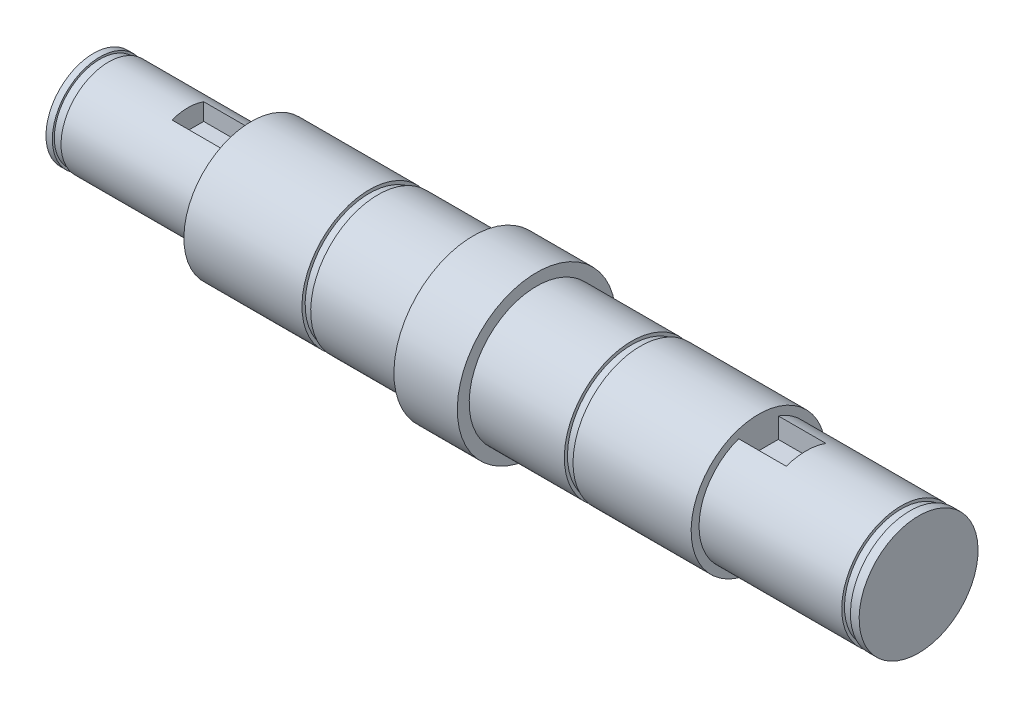
SolidWorks part; units mm, degrees
ref_plane "Front Plane" through (0, 0, 0) normal (0, 0, 1) x (1, 0, 0)
ref_plane "Top Plane" through (0, 0, 0) normal (0, 1, 0) x (1, 0, 0)
ref_plane "Right Plane" through (0, 0, 0) normal (1, 0, 0) x (0, 0, -1)
sketch "Sketch1" plane through (0, 0, 0) normal (0, 0, 1) x (1, 0, 0)
  line L0 (-52.05, 0) -> (52.05, 0)
  line L17 (-52.05, 0) -> (-52.05, 6)
  line L18 (-52.05, 6) -> (-51.25, 6)
  line L19 (-32.15, 6) -> (-32.15, 8.5)
  line L20 (-32.15, 8.5) -> (-17.25, 8.5)
  line L22 (-4.15, 8.5) -> (-4.15, 10)
  line L23 (-4.15, 10) -> (3.85, 10)
  line L24 (3.85, 10) -> (3.85, 8.5)
  line L25 (3.85, 8.5) -> (15.85, 8.5)
  line L26 (31.85, 8.5) -> (31.85, 7.5)
  line L27 (31.85, 7.5) -> (49.85, 7.5)
  line L28 (52.05, 7.5) -> (52.05, 0)
  line L29 (-50.15, 6) -> (-32.15, 6)
  line L31 (-51.25, 6) -> (-51.25, 5.75)
  line L32 (-51.25, 5.75) -> (-50.15, 5.75)
  line L33 (-50.15, 6) -> (-50.15, 5.75)
  line L34 (50.95, 7.5) -> (52.05, 7.5)
  line L36 (49.85, 7.5) -> (49.85, 7.15)
  line L37 (49.85, 7.15) -> (50.95, 7.15)
  line L38 (50.95, 7.5) -> (50.95, 7.15)
  line L39 (-16.15, 8.5) -> (-4.15, 8.5)
  line L41 (-17.25, 8.5) -> (-17.25, 8.1)
  line L42 (-17.25, 8.1) -> (-16.15, 8.1)
  line L43 (-16.15, 8.5) -> (-16.15, 8.1)
  line L44 (16.95, 8.5) -> (31.85, 8.5)
  line L46 (15.85, 8.5) -> (15.85, 8.1)
  line L47 (15.85, 8.1) -> (16.95, 8.1)
  line L48 (16.95, 8.5) -> (16.95, 8.1)
  point P4 (0, 0)
  dimension "D1" = 104.1
  dimension "D2" = 6
  dimension "D3" = 8.5
  dimension "D4" = 10
  dimension "D5" = 8.5
  dimension "D6" = 7.5
  dimension "D7" = 19.9
  dimension "D8" = 28
  dimension "D9" = 8
  dimension "D10" = 28
  dimension "D11" = 20.2
  dimension "D12" = 1.1
  dimension "D13" = 0.8
  dimension "D14" = 0.25
  dimension "D15" = 1.1
  dimension "D16" = 1.1
  dimension "D17" = 0.35
  dimension "D18" = 12
  dimension "D19" = 1.1
  dimension "D20" = 0.4
  dimension "D21" = 12
  dimension "D22" = 1.1
  dimension "D23" = 0.4
revolve "Revolve1" add sketch "Sketch1" angle 360 about L0
sketch "Sketch2" plane through (-32.15, 0, 0) normal (-1, 0, 0) x (0, 0, 1)
  line L0 (0, 6) -> (0, 0) construction
  line L1 (-2, 3.5) -> (2, 3.5)
  line L2 (-2, 3.5) -> (-2, 6)
  line L3 (-2, 6) -> (2, 6)
  line L4 (2, 3.5) -> (2, 6)
  circle A0 centre (0, 0) radius 6 construction
  circle A1 centre (0, 0) radius 6 construction
  point P11 (-2, 7.1421)
  dimension "D1" = 4
  dimension "D2" = 2.5
extrude "Cut-Extrude1" cut sketch "Sketch2" along normal blind 8
sketch "Sketch3" plane through (31.85, 0, 0) normal (1, 0, 0) x (0, 0, -1)
  line L0 (0, 0) -> (0, 7.5) construction
  line L1 (-2.5, 7.5) -> (2.5, 7.5)
  line L2 (-2.5, 7.5) -> (-2.5, 4.5)
  line L3 (-2.5, 4.5) -> (2.5, 4.5)
  line L4 (2.5, 7.5) -> (2.5, 4.5)
  circle A0 centre (0, 0) radius 7.5 construction
  dimension "D1" = 5
  dimension "D2" = 3
extrude "Cut-Extrude2" cut sketch "Sketch3" along normal blind 6
